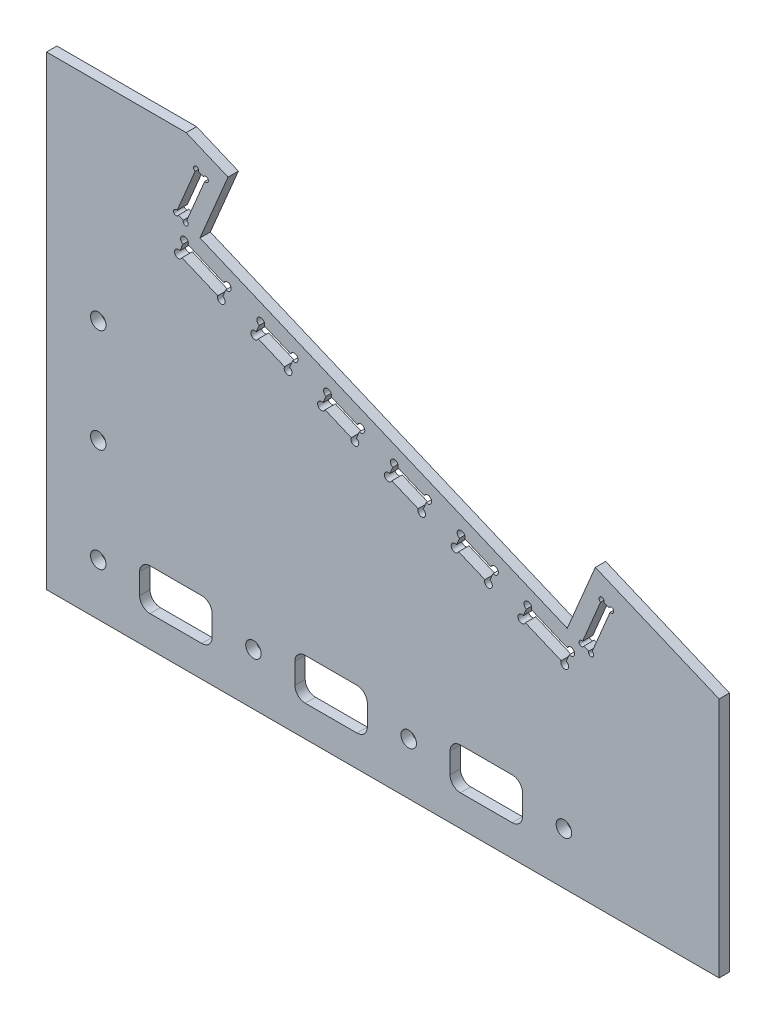
SolidWorks part; units mm, degrees
material "Thornel Mat VMA"
ref_plane "前视基准面" through (0, 0, 0) normal (0, 0, 1) x (1, 0, 0)
ref_plane "上视基准面" through (0, 0, 0) normal (0, 1, 0) x (1, 0, 0)
ref_plane "右视基准面" through (0, 0, 0) normal (1, 0, 0) x (0, 0, -1)
sketch "草图1" plane through (0, 0, 0) normal (0, 0, 1) x (1, 0, 0)
  line L1 (0, 0) -> (130, 0)
  line L2 (0, 0) -> (0, 90)
  line L3 (0, 90) -> (130, 90)
  line L4 (130, 0) -> (130, 90)
  circle A0 centre (10, 10) radius 1.5
  circle A1 centre (10, 30) radius 1.5
  circle A2 centre (10, 50) radius 1.5
  circle A3 centre (40, 10) radius 1.5
  circle A4 centre (70, 10) radius 1.5
  circle A5 centre (100, 10) radius 1.5
  dimension "D3" = 3
  dimension "D1" = 90
  dimension "D2" = 130
  dimension "D4" = 10
  dimension "D5" = 10
  dimension "D6" = 20
  dimension "D7" = 20
  dimension "D8" = 30
  dimension "D9" = 30
  dimension "D10" = 30
extrude "凸台-拉伸1" add sketch "草图1" along normal blind 2
sketch "草图2" plane through (0, 0, 2) normal (0, 0, 1) x (1, 0, 0)
  line L0 (27, 90) -> (130, 46.7028)
  line L1 (130, 90) -> (0, 90) construction
  line L2 (130, 0) -> (130, 90) construction
  line L3 (0, 90) -> (0, 0) construction
  line L4 (27, 90) -> (130, 90)
  line L5 (130, 90) -> (130, 46.7028)
  dimension "D1" = 27
  dimension "D2" = 22.8
extrude "切除-拉伸1" cut sketch "草图2" against normal through all
sketch "草图3" plane through (0, 0, 2) normal (0, 0, 1) x (1, 0, 0)
  line L0 (35.0847, 86.6015) -> (106.0682, 56.7628)
  line L1 (35.0847, 86.6015) -> (29.6595, 73.6954)
  line L2 (106.0682, 56.7628) -> (100.643, 43.8567)
  line L3 (29.6595, 73.6954) -> (100.643, 43.8567)
  line L4 (27, 90) -> (130, 46.7028) construction
  dimension "D1" = 14
  dimension "D2" = 77
  dimension "D3" = 8.77
extrude "切除-拉伸2" cut sketch "草图3" against normal through all
sketch "草图4" plane through (0, 0, 2) normal (0, 0, 1) x (1, 0, 0)
  line L0 (25.7314, 72.0924) -> (102.246, 39.9286) construction
  line L1 (29.6595, 73.6954) -> (100.643, 43.8567) construction
  line L2 (35.0847, 86.6015) -> (29.6595, 73.6954) construction
  line L3 (100.643, 43.8567) -> (106.0682, 56.7628) construction
  line L4 (25.7314, 72.0924) -> (32.3192, 87.764) construction
  line L5 (27, 90) -> (35.0847, 86.6015) construction
  line L6 (102.246, 39.9286) -> (108.8338, 55.6002) construction
  line L7 (106.0682, 56.7628) -> (130, 46.7028) construction
  line L8 (30.7691, 84.0766) -> (26.8939, 74.858)
  line L9 (30.7691, 84.0766) -> (28.9161, 84.8555)
  line L10 (26.8939, 74.858) -> (25.041, 75.6369)
  line L11 (28.9161, 84.8555) -> (25.041, 75.6369)
  line L12 (107.2837, 51.9128) -> (103.4086, 42.6942)
  line L13 (107.2837, 51.9128) -> (109.1275, 51.1378)
  line L14 (103.4086, 42.6942) -> (105.2523, 41.9191)
  line L15 (109.1275, 51.1378) -> (105.2523, 41.9191)
  line L16 (26.6532, 71.7048) -> (34.95, 68.2172)
  line L17 (26.6532, 71.7048) -> (25.4907, 68.9393)
  line L18 (34.95, 68.2172) -> (33.7875, 65.4516)
  line L19 (25.4907, 68.9393) -> (33.7875, 65.4516)
  line L20 (41.4031, 65.5046) -> (47.8561, 62.792)
  line L21 (41.4031, 65.5046) -> (40.2405, 62.739)
  line L22 (47.8561, 62.792) -> (46.6936, 60.0264)
  line L23 (40.2405, 62.739) -> (46.6936, 60.0264)
  line L24 (80.1213, 49.2289) -> (86.5744, 46.5163)
  line L25 (80.1213, 49.2289) -> (78.9588, 46.4634)
  line L26 (86.5744, 46.5163) -> (85.4118, 43.7507)
  line L27 (78.9588, 46.4634) -> (85.4118, 43.7507)
  line L28 (93.0274, 43.8037) -> (101.3242, 40.3161)
  line L29 (93.0274, 43.8037) -> (91.8648, 41.0381)
  line L30 (101.3242, 40.3161) -> (100.1616, 37.5505)
  line L31 (91.8648, 41.0381) -> (100.1616, 37.5505)
  line L32 (54.3091, 60.0794) -> (60.7622, 57.3668)
  line L37 (54.3091, 60.0794) -> (53.1466, 57.3138)
  line L38 (60.7622, 57.3668) -> (59.5996, 54.6012)
  line L39 (53.1466, 57.3138) -> (59.5996, 54.6012)
  line L40 (67.2152, 54.6542) -> (73.6683, 51.9416)
  line L41 (67.2152, 54.6542) -> (66.0527, 51.8886)
  line L42 (73.6683, 51.9416) -> (72.5057, 49.176)
  line L43 (66.0527, 51.8886) -> (72.5057, 49.176)
  point P21 (26.072, 70.3221)
  point P37 (34.3687, 66.8344)
  dimension "D1" = 3
  dimension "D2" = 3
  dimension "D3" = 3
  dimension "D4" = 1
  dimension "D5" = 2
  dimension "D6" = 9
  dimension "D7" = 9
  dimension "D8" = 1.5
  dimension "D9" = 7
  dimension "D10" = 7
  dimension "D11" = 7
  dimension "D12" = 7
  dimension "D13" = 1
  dimension "D14" = 3
  dimension "D15" = 3
  dimension "D16" = 3
  dimension "D17" = 3
  dimension "D18" = 10
  dimension "D19" = 2.01
  dimension "D20" = 3
  dimension "D21" = 10
  dimension "D22" = 7
  dimension "D23" = 7
  dimension "D24" = 3
  dimension "D25" = 7
  dimension "D26" = 7
  dimension "D27" = 3
extrude "切除-拉伸3" cut sketch "草图4" against normal through all
sketch "草图5" plane through (0, 0, 2) normal (0, 0, 1) x (1, 0, 0)
  line L0 (116.4563, 48.057) -> (112.5811, 38.8384)
  line L1 (116.4563, 48.057) -> (119.2219, 46.8945)
  line L2 (112.5811, 38.8384) -> (115.3467, 37.6758)
  line L3 (119.2219, 46.8945) -> (115.3467, 37.6758)
  line L4 (103.4086, 42.6942) -> (105.2523, 41.9191) construction
  line L5 (105.2523, 41.9191) -> (109.1275, 51.1378) construction
  dimension "D1" = 7.95
  dimension "D2" = 3
  dimension "D3" = 10
extrude "切除-拉伸4" [suppressed] cut sketch "草图5" against normal through all
sketch "草图6" plane through (0, 0, 2) normal (0, 0, 1) x (1, 0, 0)
  circle A0 centre (25.4907, 68.9393) radius 0.75
  circle A1 centre (26.6532, 71.7048) radius 0.75
  circle A2 centre (34.95, 68.2172) radius 0.75
  circle A3 centre (33.7875, 65.4516) radius 0.75
  circle A4 centre (46.6936, 60.0264) radius 0.75
  circle A5 centre (40.2405, 62.739) radius 0.75
  circle A6 centre (41.4031, 65.5046) radius 0.75
  circle A7 centre (47.8561, 62.792) radius 0.75
  circle A8 centre (80.1213, 49.2289) radius 0.75
  circle A9 centre (78.9588, 46.4634) radius 0.75
  circle A10 centre (85.4118, 43.7507) radius 0.75
  circle A11 centre (86.5744, 46.5163) radius 0.75
  circle A12 centre (100.1616, 37.5505) radius 0.75
  circle A13 centre (101.3242, 40.3161) radius 0.75
  circle A14 centre (93.0274, 43.8037) radius 0.75
  circle A15 centre (91.8648, 41.0381) radius 0.75
  circle A16 centre (26.8939, 74.858) radius 0.5
  circle A17 centre (25.041, 75.6369) radius 0.5
  circle A18 centre (28.9161, 84.8555) radius 0.5
  circle A19 centre (30.7691, 84.0766) radius 0.5
  circle A20 centre (105.2523, 41.9191) radius 0.5
  circle A21 centre (103.4086, 42.6942) radius 0.5
  circle A22 centre (107.2837, 51.9128) radius 0.5
  circle A23 centre (109.1275, 51.1378) radius 0.5
  circle A24 centre (54.3091, 60.0794) radius 0.75
  circle A25 centre (60.7622, 57.3668) radius 0.75
  circle A26 centre (53.1466, 57.3138) radius 0.75
  circle A27 centre (59.5996, 54.6012) radius 0.75
  circle A28 centre (67.2152, 54.6542) radius 0.75
  circle A29 centre (73.6683, 51.9416) radius 0.75
  circle A30 centre (72.5057, 49.176) radius 0.75
  circle A31 centre (66.0527, 51.8886) radius 0.75
  dimension "D1" = 1
  dimension "D2" = 1.5
  dimension "D3" = 1.5
  dimension "D4" = 1.5
  dimension "D5" = 1.5
  dimension "D6" = 1.5
  dimension "D7" = 1.5
  dimension "D8" = 1.5
  dimension "D9" = 1.5
  dimension "D10" = 1.5
extrude "切除-拉伸5" cut sketch "草图6" against normal blind 10
sketch "草图7" plane through (0, 0, 2) normal (0, 0, 1) x (1, 0, 0)
  line L0 (0, 20) -> (130, 20) construction
  line L1 (0, 90) -> (0, 0) construction
  line L2 (130, 0) -> (130, 46.7028) construction
  line L3 (0, 0) -> (130, 0) construction
  line L4 (130, 20) -> (109.6424, 55.2603)
  line L5 (106.0682, 56.7628) -> (130, 46.7028) construction
  line L6 (109.6424, 55.2603) -> (130, 46.7028)
  line L7 (130, 46.7028) -> (130, 20)
  dimension "D1" = 20
  dimension "D2" = 60
extrude "切除-拉伸6" [suppressed] cut sketch "草图7" against normal blind 10
fillet "圆角1" [suppressed] radius 2
sketch "草图8" plane through (0, 0, 0) normal (0, 0, -1) x (-1, 0, 0)
  line L0 (-90, 14) -> (-80, 14) construction
  line L1 (-92, 8) -> (-92, 12) construction
  line L2 (-80, 6) -> (-90, 6) construction
  line L3 (-78, 12) -> (-78, 8) construction
  line L4 (-62, 8) -> (-62, 12) construction
  line L5 (-50, 6) -> (-60, 6) construction
  line L6 (-60, 14) -> (-50, 14) construction
  line L7 (-48, 12) -> (-48, 8) construction
  line L8 (-30, 14) -> (-20, 14) construction
  line L9 (-32, 8) -> (-32, 12) construction
  line L10 (-20, 6) -> (-30, 6) construction
  line L11 (-18, 12) -> (-18, 8) construction
  line L12 (-90, 14) -> (-80, 14)
  line L13 (-92, 8) -> (-92, 12)
  line L14 (-80, 6) -> (-90, 6)
  line L15 (-78, 12) -> (-78, 8)
  line L16 (-62, 8) -> (-62, 12)
  line L17 (-50, 6) -> (-60, 6)
  line L18 (-60, 14) -> (-50, 14)
  line L19 (-48, 12) -> (-48, 8)
  line L20 (-30, 14) -> (-20, 14)
  line L21 (-32, 8) -> (-32, 12)
  line L22 (-20, 6) -> (-30, 6)
  line L23 (-18, 12) -> (-18, 8)
  arc A0 (-78, 12) -> (-80, 14) centre (-80, 12) ccw construction
  arc A1 (-90, 14) -> (-92, 12) centre (-90, 12) ccw construction
  arc A2 (-92, 8) -> (-90, 6) centre (-90, 8) ccw construction
  arc A3 (-80, 6) -> (-78, 8) centre (-80, 8) ccw construction
  arc A4 (-60, 14) -> (-62, 12) centre (-60, 12) ccw construction
  arc A5 (-62, 8) -> (-60, 6) centre (-60, 8) ccw construction
  arc A6 (-48, 12) -> (-50, 14) centre (-50, 12) ccw construction
  arc A7 (-50, 6) -> (-48, 8) centre (-50, 8) ccw construction
  arc A8 (-30, 14) -> (-32, 12) centre (-30, 12) ccw construction
  arc A9 (-32, 8) -> (-30, 6) centre (-30, 8) ccw construction
  arc A10 (-18, 12) -> (-20, 14) centre (-20, 12) ccw construction
  arc A11 (-20, 6) -> (-18, 8) centre (-20, 8) ccw construction
  arc A12 (-78, 12) -> (-80, 14) centre (-80, 12) ccw
  arc A13 (-90, 14) -> (-92, 12) centre (-90, 12) ccw
  arc A14 (-92, 8) -> (-90, 6) centre (-90, 8) ccw
  arc A15 (-80, 6) -> (-78, 8) centre (-80, 8) ccw
  arc A16 (-60, 14) -> (-62, 12) centre (-60, 12) ccw
  arc A17 (-62, 8) -> (-60, 6) centre (-60, 8) ccw
  arc A18 (-48, 12) -> (-50, 14) centre (-50, 12) ccw
  arc A19 (-50, 6) -> (-48, 8) centre (-50, 8) ccw
  arc A20 (-30, 14) -> (-32, 12) centre (-30, 12) ccw
  arc A21 (-32, 8) -> (-30, 6) centre (-30, 8) ccw
  arc A22 (-18, 12) -> (-20, 14) centre (-20, 12) ccw
  arc A23 (-20, 6) -> (-18, 8) centre (-20, 8) ccw
extrude "切除-拉伸7" cut sketch "草图8" against normal through all
